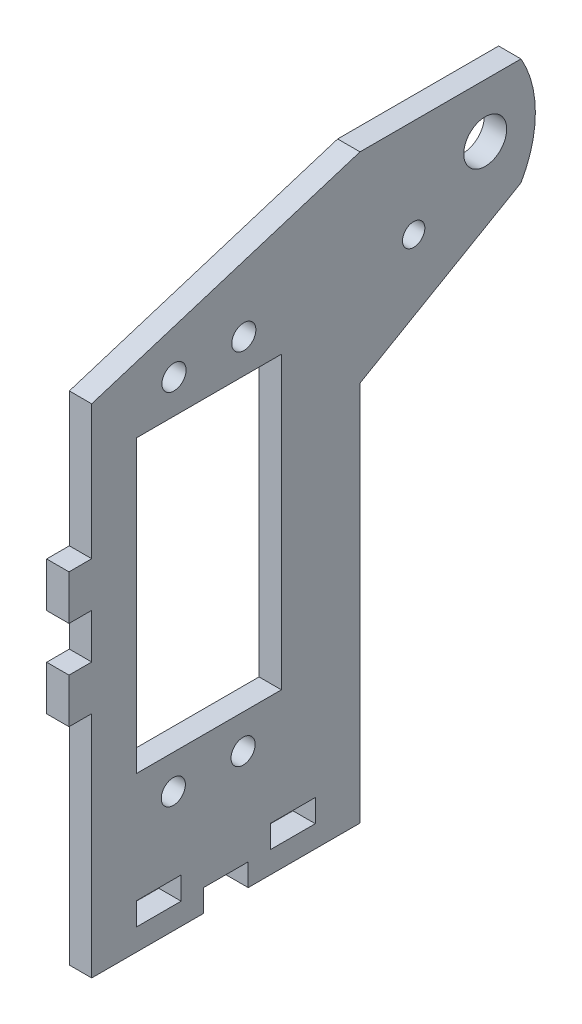
SolidWorks part; units mm, degrees
ref_plane "Front Plane" through (0, 0, 0) normal (0, 0, 1) x (1, 0, 0)
ref_plane "Top Plane" through (0, 0, 0) normal (0, 1, 0) x (1, 0, 0)
ref_plane "Right Plane" through (0, 0, 0) normal (1, 0, 0) x (0, 0, -1)
sketch "Sketch1" plane through (0, 0, 0) normal (1, 0, 0) x (0, 0, -1)
  line L0 (-8.9013, 27.9173) -> (29.1987, 27.9173)
  line L1 (-8.9013, -54.6327) -> (29.1987, -54.6327)
  line L2 (-8.9013, -54.6327) -> (-8.9013, 27.9173)
  line L3 (29.1987, 27.9173) -> (52.0587, 27.9173)
  line L4 (29.1987, -54.6327) -> (29.1987, -0.5209)
  line L7 (52.0587, 27.9173) -> (52.0587, 12.6773) construction
  line L8 (52.0587, 12.6773) -> (29.1987, -0.5209)
  arc A0 (52.0587, 27.9173) -> (52.0587, 12.6773) centre (38.8604, 20.2973) cw
  point P0 (0, 0)
  dimension "D4" = 15.24
  dimension "D5" = 120
  dimension "D3" = 38.1
  dimension "D6" = 15.24
  dimension "D1" = 38.1
  dimension "D2" = 82.55
  dimension "D7" = 22.86
extrude "Boss-Extrude1" add sketch "Sketch1" along normal blind 3.175
sketch "Sketch2" plane through (3.175, 0, 0) normal (1, 0, 0) x (0, 0, -1)
  line L1 (-8.9013, 27.9173) -> (-8.9013, -54.6327) construction
  line L2 (52.0587, 27.9173) -> (-8.9013, 27.9173) construction
  line B0 (-2.5513, -32.6617) -> (18.0347, -32.6617)
  line B1 (18.0347, -32.6617) -> (18.0347, 8.6133)
  line B2 (18.0347, 8.6133) -> (-2.5513, 8.6133)
  line B3 (-2.5513, 8.6133) -> (-2.5513, -32.6617)
  circle B4 centre (12.6967, 13.4393) radius 1.7145
  circle B5 centre (2.7867, 13.4393) radius 1.7145
  circle B6 centre (12.5955, -37.4877) radius 1.7145
  circle B7 centre (2.6855, -37.4877) radius 1.7145
  dimension "D1" = 19.304
  dimension "D2" = 6.35
sketch_block_instance "block_servo_holes_standard-1"
sketch_block "block_servo_holes_standard" parameters "D1"=3.429, "D2"=3.429, "D3"=3.429, "D4"=3.429, "D5"=3.429, "D6"=13.1735, "D7"=41.336, "D8"=20.586, "D9"=20.586, "D10"=50.292
extrude "cut for motor" cut sketch "Sketch2" against normal through all
sketch "Sketch3" plane through (3.175, 0, 0) normal (1, 0, 0) x (0, 0, -1)
  line L2 (-8.9013, 27.9173) -> (-8.9013, -54.6327) construction
  line L3 (52.0587, 27.9173) -> (-8.9013, 27.9173) construction
  circle A0 centre (46.9787, 20.2973) radius 3.048
  dimension "D1" = 7.62
  dimension "D3" = 6.096
  dimension "D2" = 55.88
extrude "cut for axle" cut sketch "Sketch3" against normal through all
sketch "Sketch4" plane through (3.175, 0, 0) normal (1, 0, 0) x (0, 0, -1)
  line L0 (10.1487, -54.6327) -> (10.1487, -49.921) construction
  line L1 (-2.5513, -51.5339) -> (3.7987, -51.5339)
  line L2 (-2.5513, -51.5339) -> (-2.5513, -48.3081)
  line L3 (-2.5513, -48.3081) -> (3.7987, -48.3081)
  line L4 (3.7987, -51.5339) -> (3.7987, -48.3081)
  line L5 (-2.5513, -51.5339) -> (3.7987, -48.3081) construction
  line L6 (-2.5513, -48.3081) -> (3.7987, -51.5339) construction
  line L7 (16.4987, -51.5339) -> (22.8487, -51.5339)
  line L8 (16.4987, -51.5339) -> (16.4987, -48.3081)
  line L9 (16.4987, -48.3081) -> (22.8487, -48.3081)
  line L10 (22.8487, -51.5339) -> (22.8487, -48.3081)
  line L11 (16.4987, -51.5339) -> (22.8487, -48.3081) construction
  line L12 (16.4987, -48.3081) -> (22.8487, -51.5339) construction
  line L13 (-8.9013, -54.6327) -> (29.1987, -54.6327) construction
  line L14 (10.1487, -49.921) -> (3.7987, -49.921) construction
  line L15 (10.1487, -49.921) -> (16.4987, -49.921) construction
  line L16 (10.1487, -54.6327) -> (13.3237, -54.6327)
  line L17 (13.3237, -54.6327) -> (13.3237, -51.4577)
  line L18 (13.3237, -51.4577) -> (6.9737, -51.4577)
  line L19 (6.9737, -51.4577) -> (6.9737, -54.6327)
  line L20 (6.9737, -54.6327) -> (10.1487, -54.6327)
  point P0 (0.6237, -49.921)
  point P5 (19.6737, -49.921)
  dimension "D1" = 6.35
  dimension "D2" = 3.0988
  dimension "D3" = 6.35
  dimension "D4" = 6.35
  dimension "D5" = 3.2258
  dimension "D6" = 3.2258
  dimension "D7" = 6.35
  dimension "D8" = 3.175
extrude "cut for tabs" cut sketch "Sketch4" against normal through all
sketch "Sketch8" plane through (3.175, 0, 0) normal (1, 0, 0) x (0, 0, -1)
  line L0 (29.1987, 27.9173) -> (-8.9013, 15.9793)
  line L3 (52.0587, 27.9173) -> (-8.9013, 27.9173) construction
  line L4 (-8.9013, 27.9173) -> (-8.9013, -54.6327) construction
  line L5 (-8.9013, 15.9793) -> (-8.9013, 27.9173)
  line L6 (-8.9013, 27.9173) -> (29.1987, 27.9173)
  dimension "D1" = 38.1
  dimension "D2" = 11.938
extrude "Cut-Extrude6" cut sketch "Sketch8" against normal through all
sketch "Sketch9" plane through (3.175, 0, 0) normal (1, 0, 0) x (0, 0, -1)
  line L0 (-8.9013, -3.0707) -> (-12.1271, -3.0707)
  line L1 (-8.9013, 15.9793) -> (-8.9013, -54.6327) construction
  line L2 (-12.1271, -3.0707) -> (-12.1271, -9.4207)
  line L3 (-12.1271, -9.4207) -> (-8.9013, -9.4207)
  line L4 (-8.9013, -9.4207) -> (-8.9013, -3.0707)
  line L5 (-8.9013, -15.7707) -> (-12.1271, -15.7707)
  line L6 (-12.1271, -15.7707) -> (-12.1271, -22.1207)
  line L7 (-12.1271, -22.1207) -> (-8.9013, -22.1207)
  line L8 (-8.9013, -22.1207) -> (-8.9013, -15.7707)
  dimension "D1" = 3.2258
  dimension "D2" = 3.2258
  dimension "D3" = 6.35
  dimension "D4" = 6.35
  dimension "D5" = 6.35
  dimension "D6" = 19.05
extrude "tabs for back plate" add sketch "Sketch9" against normal blind 3.175
sketch "Sketch10" plane through (3.175, 0, 0) normal (1, 0, 0) x (0, 0, -1)
  circle A0 centre (36.8187, 13.9473) radius 1.5875
  circle A1 centre (46.9787, 20.2973) radius 3.048 construction
  dimension "D1" = 3.175
  dimension "D2" = 10.16
  dimension "D3" = 6.35
extrude "cut for basic tilt lock screw" cut sketch "Sketch10" against normal through all
